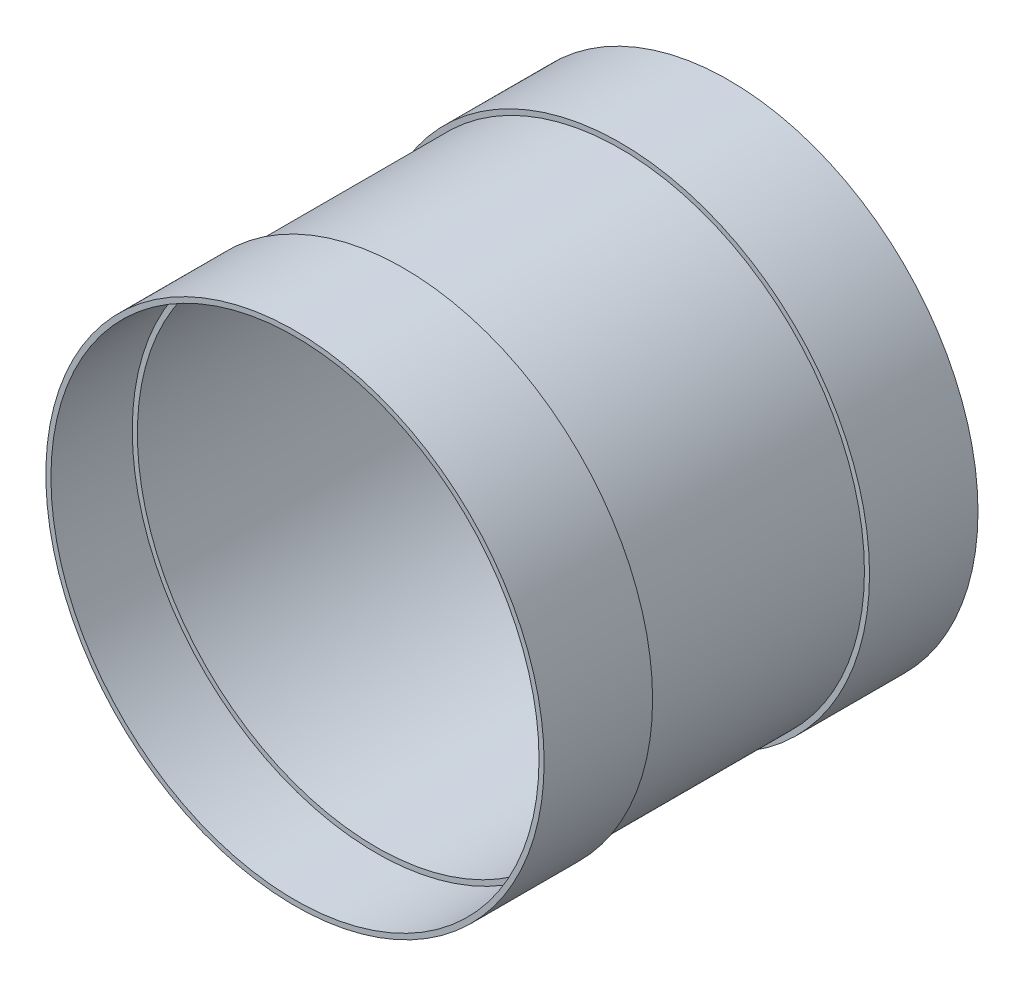
SolidWorks part; units mm, degrees
ref_plane "Front" through (0, 0, 0) normal (0, 0, 1) x (1, 0, 0)
ref_plane "Top" through (0, 0, 0) normal (0, 1, 0) x (1, 0, 0)
ref_plane "Right" through (0, 0, 0) normal (1, 0, 0) x (0, 0, -1)
sketch "Sketch2" plane through (0, 0, 0) normal (1, 0, 0) x (0, 0, -1)
  line L0 (-62.5946, 0) -> (53.5645, 0) construction
  line L1 (-203.2, 233.3625) -> (-101.6, 233.3625)
  line L2 (-101.6, 233.3625) -> (-101.6, 228.6)
  line L7 (-101.6, 228.6) -> (-203.2, 228.6)
  line L8 (-203.2, 228.6) -> (-203.2, 233.3625)
  line L9 (0, 0) -> (0, 72.5353) construction
  line L11 (101.6, 233.3625) -> (203.2, 233.3625)
  line L12 (101.6, 233.3625) -> (101.6, 228.6)
  line L13 (101.6, 228.6) -> (203.2, 228.6)
  line L14 (203.2, 233.3625) -> (203.2, 228.6)
  point P13 (203.2, 230.9812)
  dimension "D1" = 101.6
  dimension "D2" = 4.7625
  dimension "D3" = 406.4
  dimension "D4" = 457.2
revolve "Revolve1" add sketch "Sketch2" angle 360 about L0
sketch "Sketch3" plane through (0, 0, 0) normal (1, 0, 0) x (0, 0, -1)
  line L1 (-127, 223.8375) -> (127, 223.8375)
  line L2 (-127, 223.8375) -> (-127, 228.6)
  line L3 (-127, 228.6) -> (127, 228.6)
  line L4 (127, 223.8375) -> (127, 228.6)
  line L6 (0, 0) -> (103.0496, 0) construction
  line L7 (-101.6, 228.6) -> (-203.2, 228.6) construction
  line L8 (-203.2, 233.3625) -> (-203.2, -233.3625) construction
  line L9 (203.2, -233.3625) -> (203.2, 233.3625) construction
  dimension "D1" = 4.7625
  dimension "D2" = 76.2
  dimension "D3" = 76.2
revolve "Revolve2" add sketch "Sketch3" angle 360 about L6
